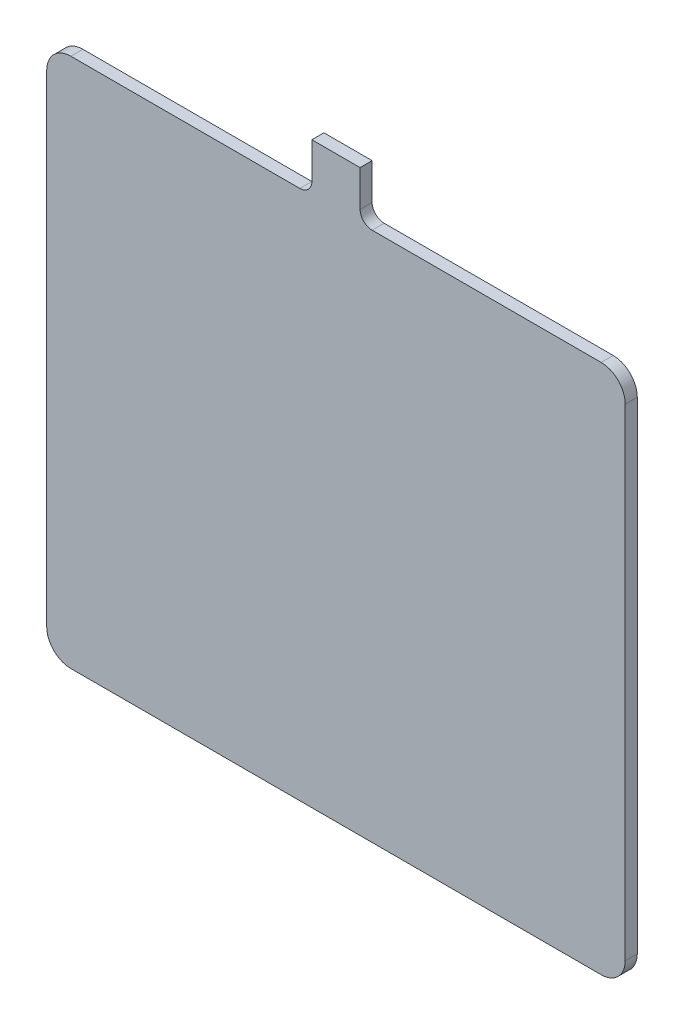
SolidWorks part; units mm, degrees
ref_plane "Plan de face" through (0, 0, 0) normal (0, 0, 1) x (1, 0, 0)
ref_plane "Plan de dessus" through (0, 0, 0) normal (0, 1, 0) x (1, 0, 0)
ref_plane "Plan de droite" through (0, 0, 0) normal (1, 0, 0) x (0, 0, -1)
sketch "Esquisse1" plane through (0, 0, 0) normal (0, 0, 1) x (1, 0, 0)
  line L1 (-220, 295) -> (-30, 295)
  line L2 (-240, 275) -> (-240, -125)
  line L3 (-220, -145) -> (220, -145)
  line L4 (240, 275) -> (240, -125)
  line L8 (-340, 335) -> (340, 335) construction
  line L9 (30, 295) -> (220, 295)
  line L10 (-20, 335) -> (20, 335)
  line L11 (-20, 305) -> (-20, 335)
  line L13 (20, 305) -> (20, 335)
  arc A0 (-30, 295) -> (-20, 305) centre (-30, 305) ccw
  arc A1 (30, 295) -> (20, 305) centre (30, 305) cw
  arc A4 (-240, -125) -> (-220, -145) centre (-220, -125) ccw
  arc A5 (220, -145) -> (240, -125) centre (220, -125) ccw
  arc A6 (220, 295) -> (240, 275) centre (220, 275) cw
  arc A7 (-220, 295) -> (-240, 275) centre (-220, 275) ccw
  dimension "D8" = 10
  dimension "D9" = 20
extrude "Boss.-Extru.1" add sketch "Esquisse1" along normal blind 10
